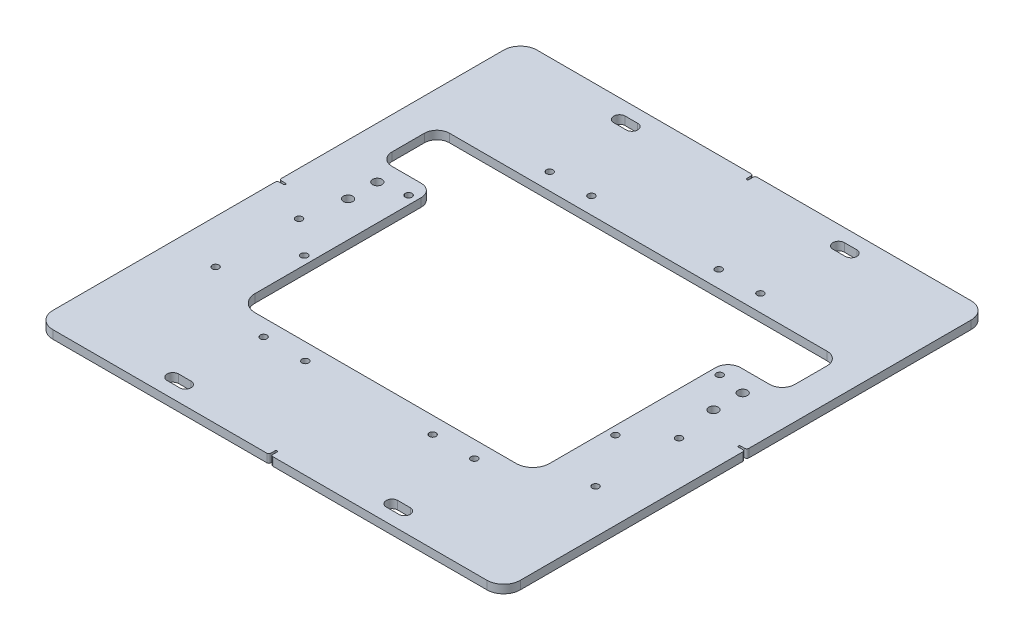
SolidWorks part; units mm, degrees
material "AISI Type 316L stainless steel"
ref_plane "Front Plane" through (0, 0, 0) normal (0, 0, 1) x (1, 0, 0)
ref_plane "Top Plane" through (0, 0, 0) normal (0, 1, 0) x (1, 0, 0)
ref_plane "Right Plane" through (0, 0, 0) normal (1, 0, 0) x (0, 0, -1)
sketch "Sketch2" plane through (0, 0, 0) normal (0, 1, 0) x (1, 0, 0)
  line L1 (-177.8, 184.15) -> (177.8, 184.15)
  line L2 (-177.8, 184.15) -> (-177.8, -184.15)
  line L3 (-177.8, -184.15) -> (177.8, -184.15)
  line L4 (177.8, 184.15) -> (177.8, -184.15)
  line L5 (-177.8, 184.15) -> (177.8, -184.15) construction
  line L6 (-177.8, -184.15) -> (177.8, 184.15) construction
  point P0 (0, 0)
  dimension "Cmain" = 355.6
  dimension "Dmain" = 368.3
extrude "Boss-Extrude1" add sketch "Sketch2" along normal blind 6.35
fillet "Fillet1" radius 12.7 4 edges at (-177.8, 3.175, -184.15) (-177.8, 3.175, 184.15) (177.8, 3.175, -184.15) (177.8, 3.175, 184.15)
sketch "Sketch3" plane through (0, 6.35, 0) normal (0, 1, 0) x (1, 0, 0)
  line L0 (165.1, 184.15) -> (-165.1, 184.15) construction
  line L1 (0, 184.15) -> (0, -184.15) construction
  line L2 (-165.1, -184.15) -> (165.1, -184.15) construction
  line L3 (-88.1062, 169.8625) -> (-78.5812, 169.8625) construction
  line L4 (-88.1062, 174.2281) -> (-78.5812, 174.2281)
  line L5 (-88.1062, 165.4969) -> (-78.5812, 165.4969)
  line L6 (88.1063, 169.8625) -> (78.5813, 169.8625) construction
  line L7 (88.1063, 165.4969) -> (78.5813, 165.4969)
  line L8 (88.1063, 174.2281) -> (78.5813, 174.2281)
  line L9 (-88.1062, -169.8625) -> (-78.5812, -169.8625) construction
  line L10 (-88.1062, -165.4969) -> (-78.5812, -165.4969)
  line L11 (-88.1062, -174.2281) -> (-78.5812, -174.2281)
  line L12 (78.5813, -169.8625) -> (88.1063, -169.8625) construction
  line L13 (78.5813, -165.4969) -> (88.1063, -165.4969)
  line L14 (78.5813, -174.2281) -> (88.1063, -174.2281)
  arc A4 (-88.1062, 174.2281) -> (-88.1062, 165.4969) centre (-88.1062, 169.8625) ccw
  arc A5 (-78.5812, 165.4969) -> (-78.5812, 174.2281) centre (-78.5812, 169.8625) ccw
  arc A6 (88.1063, 165.4969) -> (88.1063, 174.2281) centre (88.1063, 169.8625) ccw
  arc A7 (78.5813, 174.2281) -> (78.5813, 165.4969) centre (78.5813, 169.8625) ccw
  arc A8 (-88.1062, -165.4969) -> (-88.1062, -174.2281) centre (-88.1062, -169.8625) ccw
  arc A9 (-78.5812, -174.2281) -> (-78.5812, -165.4969) centre (-78.5812, -169.8625) ccw
  arc A10 (78.5813, -165.4969) -> (78.5813, -174.2281) centre (78.5813, -169.8625) ccw
  arc A11 (88.1063, -174.2281) -> (88.1063, -165.4969) centre (88.1063, -169.8625) ccw
  point P16 (-83.3437, 169.8625)
  point P23 (83.3438, 169.8625)
  point P28 (-83.3437, -169.8625)
  point P35 (83.3438, -169.8625)
  dimension "D2" = 4.3656
  dimension "D3" = 14.2875
  dimension "D5" = 88.1063
  dimension "D6" = 88.1063
  dimension "D7" = 14.2875
  dimension "D8" = 88.1063
  dimension "D11" = 14.2875
  dimension "D9" = 88.1063
  dimension "D4" = 14.2875
  dimension "D10" = 9.525
extrude "MOUNTING HOLES" cut sketch "Sketch3" against normal through all
sketch "Sketch4" plane through (0, 6.35, 0) normal (0, 1, 0) x (1, 0, 0)
  line L0 (-177.8, 171.45) -> (-177.8, -171.45) construction
  line L1 (-99.281, -96.106) -> (99.281, -96.106)
  line L2 (-111.981, -83.406) -> (-111.981, 42.8689)
  line L3 (-143.6688, 96.106) -> (143.6687, 96.106)
  line L4 (111.981, -83.406) -> (111.981, 42.8689)
  line L5 (-111.981, -96.106) -> (11.3473, 9.7387) construction
  line L6 (-11.3473, 9.7387) -> (111.981, -96.106) construction
  line L7 (-143.6688, 52.3939) -> (-121.506, 52.3939)
  line L8 (165.1, 184.15) -> (-165.1, 184.15) construction
  line L9 (-153.1938, 86.581) -> (-153.1938, 61.9189)
  line L10 (143.6687, 52.3939) -> (121.506, 52.3939)
  line L11 (153.1937, 61.9189) -> (153.1937, 86.581)
  line L12 (177.8, -171.45) -> (177.8, 171.45) construction
  line L13 (-165.1, -184.15) -> (165.1, -184.15) construction
  arc A0 (-99.281, -96.106) -> (-111.981, -83.406) centre (-99.281, -83.406) cw
  arc A1 (99.281, -96.106) -> (111.981, -83.406) centre (99.281, -83.406) ccw
  arc A4 (143.6687, 96.106) -> (153.1937, 86.581) centre (143.6687, 86.581) cw
  arc A5 (143.6687, 52.3939) -> (153.1937, 61.9189) centre (143.6687, 61.9189) ccw
  arc A6 (121.506, 52.3939) -> (111.981, 42.8689) centre (121.506, 42.8689) ccw
  arc A7 (-121.506, 52.3939) -> (-111.981, 42.8689) centre (-121.506, 42.8689) cw
  arc A8 (-153.1938, 61.9189) -> (-143.6688, 52.3939) centre (-143.6688, 61.9189) ccw
  arc A9 (-143.6688, 96.106) -> (-153.1938, 86.581) centre (-143.6688, 86.581) ccw
  point P0 (0, 0)
  point P34 (-132.5874, 52.3939)
  dimension "D3" = 12.7
  dimension "D4" = 9.525
  dimension "D1" = 65.819
  dimension "D2" = 88.044
  dimension "D5" = 131.7561
  dimension "D6" = 24.6063
  dimension "D7" = 24.6063
  dimension "D8" = 65.819
  dimension "D9" = 88.044
  dimension "D10" = 131.7561
extrude "PLUNGER CUTOUT" cut sketch "Sketch4" against normal through all
hole_wizard "1/4-20 Tapped Hole2" positions "Sketch8" profile "Sketch9" tap size "1/4-20" standard "ANSI Inch" end condition through all
sketch "Sketch8" plane through (0, 6.35, 0) normal (0, 1, 0) x (1, 0, 0)
  line L0 (165.1, 184.15) -> (-165.1, 184.15) construction
  line L1 (-177.8, 171.45) -> (-177.8, -171.45) construction
  line L2 (177.8, -171.45) -> (177.8, 171.45) construction
  line L3 (-165.1, -184.15) -> (165.1, -184.15) construction
  point P7 (-80.1675, -108.8187)
  point P9 (-48.4175, -108.8187)
  point P11 (48.4175, -108.8187)
  point P13 (80.1675, -108.8187)
  point P15 (80.1675, 108.8187)
  point P17 (48.4175, 108.8187)
  point P19 (-48.4175, 108.8187)
  point P21 (-80.1675, 108.8187)
  dimension "D3" = 31.75
  dimension "D1" = 75.3313
  dimension "D2" = 97.6325
  dimension "D4" = 97.6325
  dimension "D5" = 31.75
  dimension "D6" = 75.3313
sketch "Sketch9" plane through (-80.1675, 6.35, 108.8187) normal (1, 0, 0) x (0, 0, 1)
  line L0 (0, 0) -> (0, 6.35)
  line L1 (0, 6.35) -> (2.5527, 6.35)
  line L2 (2.5527, 6.35) -> (2.5527, 0)
  line L5 (2.5527, 0) -> (0, 0)
  line L11 (0, -6.35) -> (0, 107.95) construction
  dimension "Thru Tap Drill Dia." = 5.1054
  dimension "Thru Tap Drill Depth" = 6.35
cosmetic thread "Hole Thread9" parameters "D2"=6.35
cosmetic thread "Hole Thread10" parameters "D2"=6.35
cosmetic thread "Hole Thread11" parameters "D2"=6.35
cosmetic thread "Hole Thread12" parameters "D2"=6.35
cosmetic thread "Hole Thread13" parameters "D2"=6.35
cosmetic thread "Hole Thread14" parameters "D2"=6.35
cosmetic thread "Hole Thread15" parameters "D2"=6.35
cosmetic thread "Hole Thread16" parameters "D2"=6.35
sketch "Sketch10" plane through (0, 6.35, 0) normal (0, 1, 0) x (1, 0, 0)
  line L0 (165.1, 184.15) -> (-165.1, 184.15) construction
  line L1 (177.8, -171.45) -> (177.8, 171.45) construction
  line L2 (-165.1, -184.15) -> (165.1, -184.15) construction
  line L3 (-177.8, 171.45) -> (-177.8, -171.45) construction
  line L4 (0, 184.15) -> (0, -184.15) construction
  line L5 (-177.8, 0) -> (177.8, 0) construction
  line L6 (-0.7937, -179.3875) -> (-0.7938, -184.15)
  line L7 (-0.7938, -184.15) -> (0.7938, -184.15)
  line L8 (0.7937, -179.3875) -> (0.7938, -184.15)
  line L9 (-173.0375, 0.7937) -> (-177.8, 0.7938)
  line L10 (-177.8, 0.7938) -> (-177.8, -0.7937)
  line L11 (-173.0375, -0.7937) -> (-177.8, -0.7937)
  line L12 (173.0375, 0.7937) -> (177.8, 0.7937)
  line L13 (177.8, 0.7937) -> (177.8, -0.7938)
  line L14 (173.0375, -0.7937) -> (177.8, -0.7938)
  line L15 (-0.7937, 179.3875) -> (-0.7937, 184.15)
  line L16 (-0.7937, 184.15) -> (0.7937, 184.15)
  line L17 (0.7937, 179.3875) -> (0.7937, 184.15)
  arc A0 (-0.7937, 179.3875) -> (0.7937, 179.3875) centre (0, 179.3875) ccw
  arc A1 (-173.0375, -0.7937) -> (-173.0375, 0.7937) centre (-173.0375, 0) ccw
  arc A2 (0.7937, -179.3875) -> (-0.7937, -179.3875) centre (0, -179.3875) ccw
  arc A3 (173.0375, 0.7937) -> (173.0375, -0.7937) centre (173.0375, 0) ccw
  dimension "D1" = 1.5875
  dimension "D2" = 4.7625
  dimension "D3" = 4.7625
  dimension "D4" = 4.7625
  dimension "D5" = 4.7625
extrude "CENTERING MARKERS" cut sketch "Sketch10" against normal through all
fillet "Fillet2" radius 1.5875 8 edges at (0.7938, 3.175, 184.15) (-0.7938, 3.175, 184.15) (177.8, 3.175, -0.7937) (177.8, 3.175, 0.7938) (-0.7937, 3.175, -184.15) (0.7937, 3.175, -184.15) (-177.8, 3.175, -0.7938) (-177.8, 3.175, 0.7937)
hole_wizard "1/4-20 Tapped Hole5" positions "Sketch15" profile "Sketch16" tap size "1/4-20" standard "ANSI Inch" end condition through all
sketch "Sketch15" plane through (0, 6.35, 0) normal (0, 1, 0) x (1, 0, 0)
  line L0 (-118.3323, 39.6875) -> (118.3323, 39.6875) construction
  line L3 (-144.526, -80.9752) -> (144.526, -80.9752) construction
  line L4 (-118.3323, -39.6875) -> (118.3323, -39.6875) construction
  line L5 (-144.526, -17.4752) -> (144.526, -17.4752) construction
  line L6 (0, 39.6875) -> (0, 0) construction
  line L7 (0, 0) -> (0, -17.4752) construction
  line L8 (0, -17.4752) -> (0, -39.6875) construction
  line L9 (0, -39.6875) -> (0, -80.9752) construction
  line L11 (-165.1, -184.15) -> (-2.3813, -184.15) construction
  line L12 (177.8, 2.3813) -> (177.8, 171.45) construction
  line L13 (177.8, -171.45) -> (177.8, -2.3813) construction
  line L14 (-2.3813, 184.15) -> (-165.1, 184.15) construction
  point P0 (-144.526, -17.4752)
  point P3 (-144.526, -80.9752)
  point P6 (-118.3323, -39.6875)
  point P9 (-118.3323, 39.6875)
  point P12 (118.3323, 39.6875)
  point P15 (118.3323, -39.6875)
  point P18 (144.526, -17.4752)
  point P21 (144.526, -80.9752)
  dimension "D1" = 144.4625
  dimension "D2" = 166.6748
  dimension "D3" = 144.4625
  dimension "D4" = 103.1748
  dimension "D5" = 59.4677
  dimension "D6" = 33.274
  dimension "D7" = 59.4677
  dimension "D8" = 33.274
sketch "Sketch16" plane through (-144.526, 6.35, 17.4752) normal (1, 0, 0) x (0, 0, 1)
  line L0 (0, 0) -> (0, 6.35)
  line L1 (0, 6.35) -> (2.5527, 6.35)
  line L2 (2.5527, 6.35) -> (2.5527, 0)
  line L5 (2.5527, 0) -> (0, 0)
  line L11 (0, -6.35) -> (0, 107.95) construction
  dimension "Thru Tap Drill Dia." = 5.1054
  dimension "Thru Tap Drill Depth" = 6.35
cosmetic thread "Hole Thread25" parameters "D2"=6.35
cosmetic thread "Hole Thread26" parameters "D2"=6.35
cosmetic thread "Hole Thread27" parameters "D2"=6.35
cosmetic thread "Hole Thread28" parameters "D2"=6.35
cosmetic thread "Hole Thread29" parameters "D2"=6.35
cosmetic thread "Hole Thread30" parameters "D2"=6.35
cosmetic thread "Hole Thread31" parameters "D2"=6.35
cosmetic thread "Hole Thread32" parameters "D2"=6.35
chamfer "Chamfer1" [suppressed] distance 3.175 angle 45
sketch "Sketch17" plane through (0, 6.35, 0) normal (0, 1, 0) x (1, 0, 0)
  line L1 (-177.8, 171.45) -> (-177.8, 2.3813) construction
  line L2 (177.8, 2.3813) -> (177.8, 171.45) construction
  circle A0 centre (-138.9698, 36.5125) radius 3.5719
  circle A1 centre (-138.9698, 14.2875) radius 3.5719
  circle A2 centre (138.9698, 14.2875) radius 3.5719
  circle A3 centre (138.9698, 36.5125) radius 3.5719
  arc A4 (173.0375, 0.7937) -> (173.0375, -0.7937) centre (173.0375, 0) ccw construction
  arc A5 (-173.0375, -0.7937) -> (-173.0375, 0.7937) centre (-173.0375, 0) ccw construction
  point P17 (172.2438, 0)
  dimension "D1" = 7.1437
  dimension "D2" = 14.2875
  dimension "D3" = 38.8302
  dimension "D4" = 22.225
  dimension "D5" = 38.8302
  dimension "D7" = 22.225
  dimension "D6" = 14.2875
extrude "Cut-Extrude1" cut sketch "Sketch17" against normal through all
